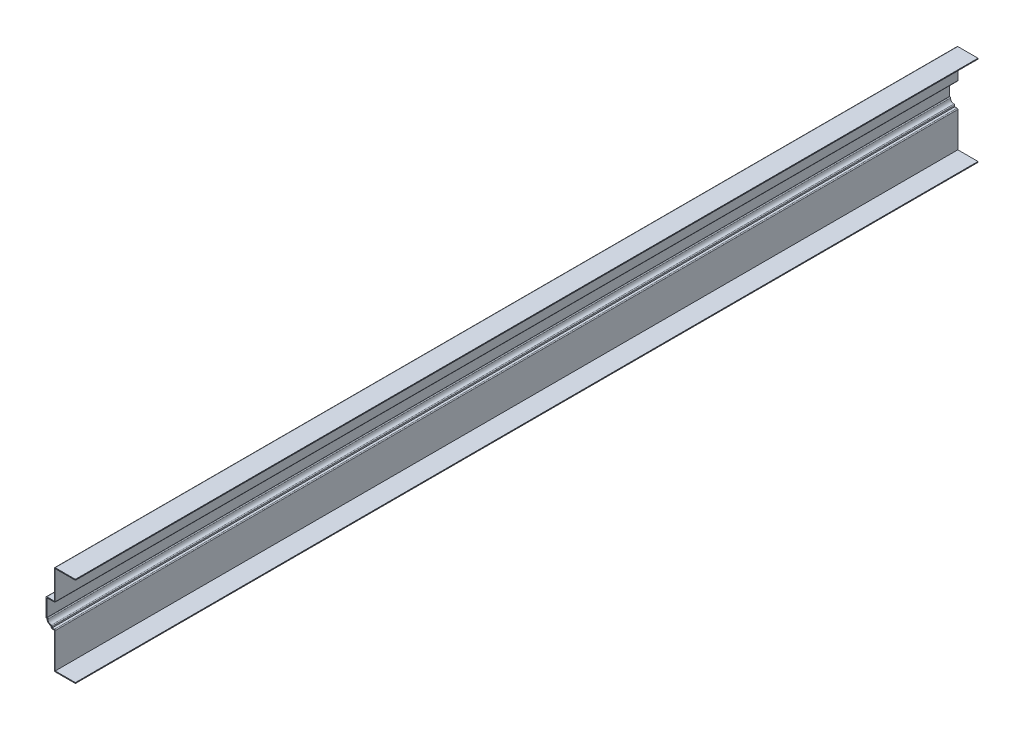
SolidWorks part; units mm, degrees
ref_plane "Front Plane" through (0, 0, 0) normal (0, 0, 1) x (1, 0, 0)
ref_plane "Top Plane" through (0, 0, 0) normal (0, 1, 0) x (1, 0, 0)
ref_plane "Right Plane" through (0, 0, 0) normal (1, 0, 0) x (0, 0, -1)
sketch "Sketch1" plane through (0, 0, 0) normal (0, 0, 1) x (1, 0, 0)
  line L0 (0, 0) -> (-31.75, 0)
  line L1 (-31.75, 0) -> (-31.75, 53.975)
  line L2 (-31.75, 53.975) -> (-36.5125, 53.975)
  line L3 (-36.5125, 53.975) -> (-36.5125, 57.15)
  line L4 (-42.8625, 63.5) -> (-44.45, 63.5)
  line L5 (-44.45, 63.5) -> (-44.45, 92.075)
  line L6 (-44.45, 92.075) -> (-31.75, 92.075)
  line L7 (-31.75, 92.075) -> (-31.75, 136.525)
  line L8 (-31.75, 136.525) -> (0, 136.525)
  arc A0 (-36.5125, 57.15) -> (-42.8625, 63.5) centre (-36.5125, 63.5) cw
  dimension "D1" = 31.75
  dimension "D2" = 53.975
  dimension "D3" = 4.7625
  dimension "D4" = 3.175
  dimension "D5" = 6.35
  dimension "D6" = 1.5875
  dimension "D7" = 28.575
  dimension "D8" = 12.7
  dimension "D9" = 44.45
  dimension "D10" = 31.75
extrude "Extrude-Thin1" add sketch "Sketch1" against normal blind 1365.25 thin
fillet "Fillet1" radius 1.27 9 edges at (-31.75, 0, -682.625) (-30.48, 55.245, -682.625) (-36.5125, 53.975, -682.625) (-35.2425, 58.5813, -682.625) (-41.4312, 64.77, -682.625) (-44.45, 63.5, -682.625) (-44.45, 92.075, -682.625) (-30.48, 90.805, -682.625) (-31.75, 136.525, -682.625)
